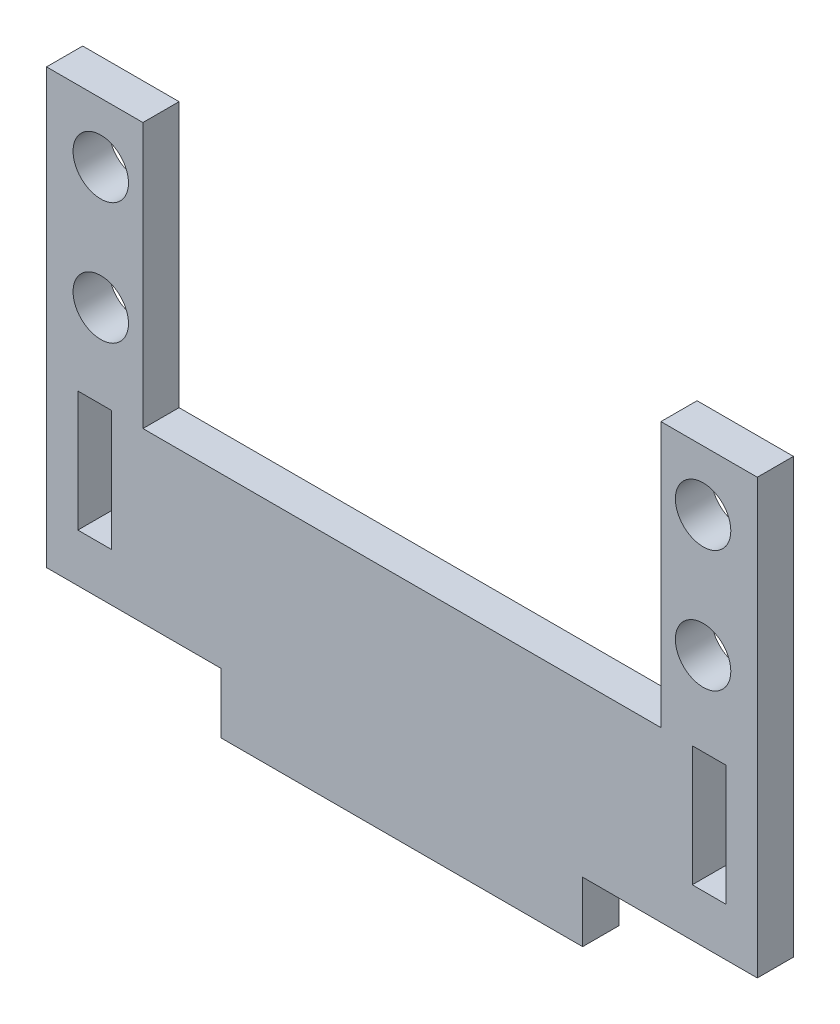
SolidWorks part; units mm, degrees
ref_plane "Front Plane" through (0, 0, 0) normal (0, 0, 1) x (1, 0, 0)
ref_plane "Top Plane" through (0, 0, 0) normal (0, 1, 0) x (1, 0, 0)
ref_plane "Right Plane" through (0, 0, 0) normal (1, 0, 0) x (0, 0, -1)
sketch "Sketch1" plane through (0, 0, 0) normal (0, 0, 1) x (1, 0, 0)
  line L1 (0, 0) -> (8, 0)
  line L2 (0, 0) -> (0, -36)
  line L3 (0, -36) -> (59, -36)
  line L4 (59, 0) -> (59, -36)
  line L8 (8, 0) -> (8, -22)
  line L9 (8, -22) -> (51, -22)
  line L10 (51, -22) -> (51, 0)
  line L14 (51, 0) -> (59, 0)
  circle A0 centre (4.5, -15.05) radius 2.3
  circle A1 centre (4.5, -4.95) radius 2.3
  circle A2 centre (54.5, -4.95) radius 2.3
  circle A3 centre (54.5, -15.05) radius 2.3
  dimension "D3" = 8
  dimension "D4" = 51
  dimension "D1" = 4.6
  dimension "D2" = 4.5
  dimension "D5" = 54.5
  dimension "D6" = 4.95
  dimension "D7" = 15.05
  dimension "D8" = 22
  dimension "D9" = 36
extrude "Boss-Extrude1" add sketch "Sketch1" along normal blind 3 contours L10 L9 L8 L1 L2 L3 L4 A3 A2 A1 A0
sketch "Sketch3" plane through (0, 0, 3) normal (0, 0, 1) x (1, 0, 0)
  line L1 (2.6, -22) -> (5.4, -22)
  line L2 (2.6, -22) -> (2.6, -32)
  line L3 (2.6, -32) -> (5.4, -32)
  line L4 (5.4, -22) -> (5.4, -32)
  line L5 (53.6, -22) -> (56.4, -22)
  line L6 (53.6, -22) -> (53.6, -32)
  line L7 (53.6, -32) -> (56.4, -32)
  line L8 (56.4, -22) -> (56.4, -32)
  line L10 (0, -36) -> (59, -36) construction
  line L11 (4, -22) -> (4, -32) construction
  line L12 (0, 0) -> (0, -36) construction
  line L13 (55, -22) -> (55, -32) construction
  line L14 (59, 0) -> (59, -36) construction
  dimension "D1" = 2.8
  dimension "D2" = 2.8
  dimension "D3" = 10
  dimension "D4" = 10
  dimension "D5" = 4
  dimension "D6" = 4
  dimension "D7" = 4
extrude "Cut-Extrude1" cut sketch "Sketch3" against normal blind 10
sketch "Sketch4" plane through (0, -36, 0) normal (0, -1, 0) x (1, 0, 0)
  line L0 (0, 3) -> (59, 3) construction
  line L1 (14.5, 3) -> (44.5, 3)
  line L2 (14.5, 3) -> (14.5, 0)
  line L3 (14.5, 0) -> (44.5, 0)
  line L4 (44.5, 3) -> (44.5, 0)
  line L5 (0, 0) -> (59, 0) construction
  line L6 (0, 3) -> (0, 0) construction
  dimension "D1" = 30
  dimension "D2" = 14.5
extrude "Boss-Extrude2" add sketch "Sketch4" along normal blind 5
